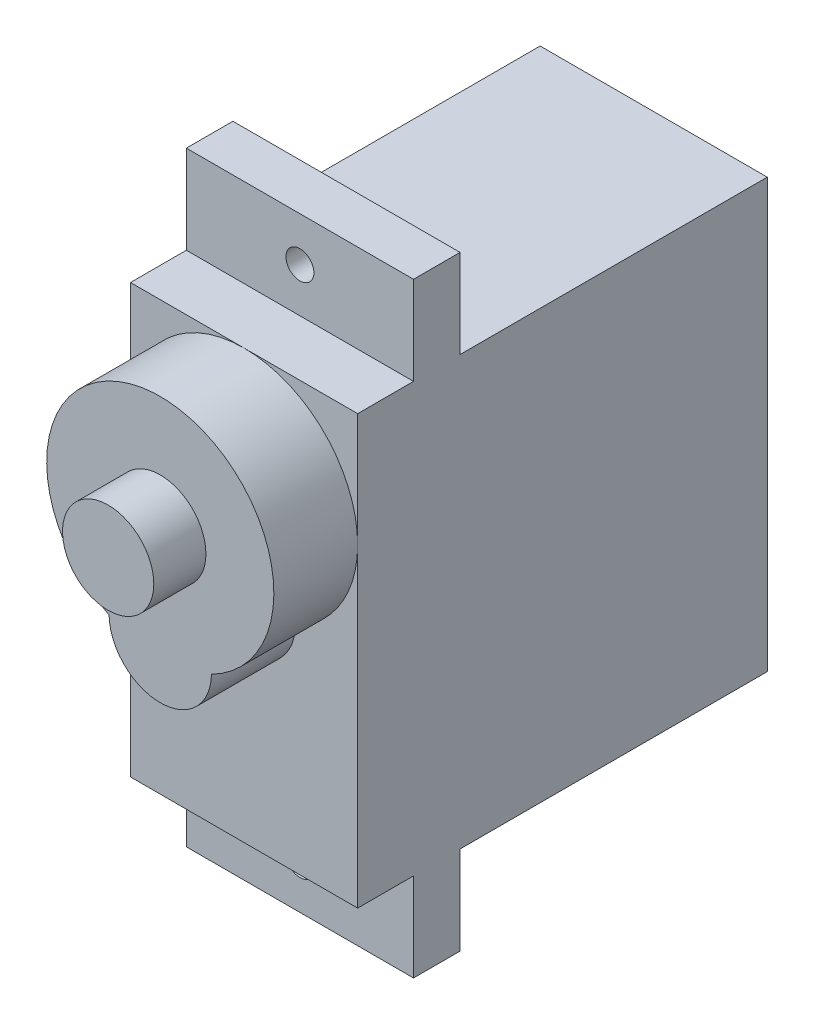
SolidWorks part; units mm, degrees
ref_plane "Plan de face" through (0, 0, 0) normal (0, 0, 1) x (1, 0, 0)
ref_plane "Plan de dessus" through (0, 0, 0) normal (0, 1, 0) x (1, 0, 0)
ref_plane "Plan de droite" through (0, 0, 0) normal (1, 0, 0) x (0, 0, -1)
sketch "Esquisse1" plane through (0, 0, 0) normal (1, 0, 0) x (0, 0, -1)
  line L1 (11, -11.5) -> (-11, -11.5)
  line L2 (11, -11.5) -> (11, 11.5)
  line L3 (11, 11.5) -> (-11, 11.5)
  line L4 (-11, -11.5) -> (-11, 11.5)
  line L5 (11, -11.5) -> (-11, 11.5) construction
  line L6 (11, 11.5) -> (-11, -11.5) construction
  point P0 (0, 0)
  dimension "D1" = 22
  dimension "D2" = 23
extrude "Boss.-Extru.1" add sketch "Esquisse1" along normal mid plane 12.2
sketch "Esquisse2" plane through (0, 0, 11) normal (0, 0, 1) x (1, 0, 0)
  line L1 (6.1, 11.5) -> (-6.1, 11.5) construction
  line L2 (-6.1, 11.5) -> (-6.1, -11.5) construction
  arc A0 (2.7496, -0.0451) -> (-2.7496, -0.0451) centre (0, 5.4) ccw
  arc A1 (-2.7496, -0.0451) -> (2.7496, -0.0451) centre (0, 0) ccw
  dimension "D1" = 2.75
extrude "Boss.-Extru.2" add sketch "Esquisse2" along normal blind 4.5
sketch "Esquisse3" plane through (0, 0, 15.5) normal (0, 0, 1) x (1, 0, 0)
  circle A0 centre (0, 5.4) radius 2.45
  arc A1 (2.7496, -0.0451) -> (-2.7496, -0.0451) centre (0, 5.4) ccw construction
  dimension "D1" = 4.9
extrude "Boss.-Extru.3" add sketch "Esquisse3" along normal blind 2.8
sketch "Esquisse4" plane through (0, 0, 0) normal (1, 0, 0) x (0, 0, -1)
  line L0 (11, 11.5) -> (-11, 11.5) construction
  line L1 (-8, 11.5) -> (-5.5, 11.5)
  line L2 (-8, 11.5) -> (-8, 16.25)
  line L3 (-8, 16.25) -> (-5.5, 16.25)
  line L4 (-5.5, 11.5) -> (-5.5, 16.25)
  line L5 (-11, -11.5) -> (11, -11.5) construction
  line L6 (-8, -11.5) -> (-5.5, -11.5)
  line L7 (-8, -11.5) -> (-8, -16.25)
  line L8 (-8, -16.25) -> (-5.5, -16.25)
  line L9 (-5.5, -11.5) -> (-5.5, -16.25)
  line L10 (11, -11.5) -> (11, 11.5) construction
  dimension "D1" = 32.5
  dimension "D2" = 16.5
  dimension "D3" = 2.5
extrude "Boss.-Extru.4" add sketch "Esquisse4" along normal mid plane 12.2
sketch "Esquisse5" plane through (0, 0, 8) normal (0, 0, 1) x (1, 0, 0)
  line L0 (-6.1, 16.25) -> (6.1, 11.5) construction
  line L1 (-6.1, -11.5) -> (6.1, -16.25) construction
  circle A0 centre (0, 13.875) radius 0.75
  circle A1 centre (0, -13.875) radius 0.75
  dimension "D1" = 1.5
extrude "Enlèv. mat.-Extru.1" cut sketch "Esquisse5" against normal up to next
ref_plane "Plan1" through (0, 0, 0) normal (0, -1, 0) x (-1, 0, 0)
